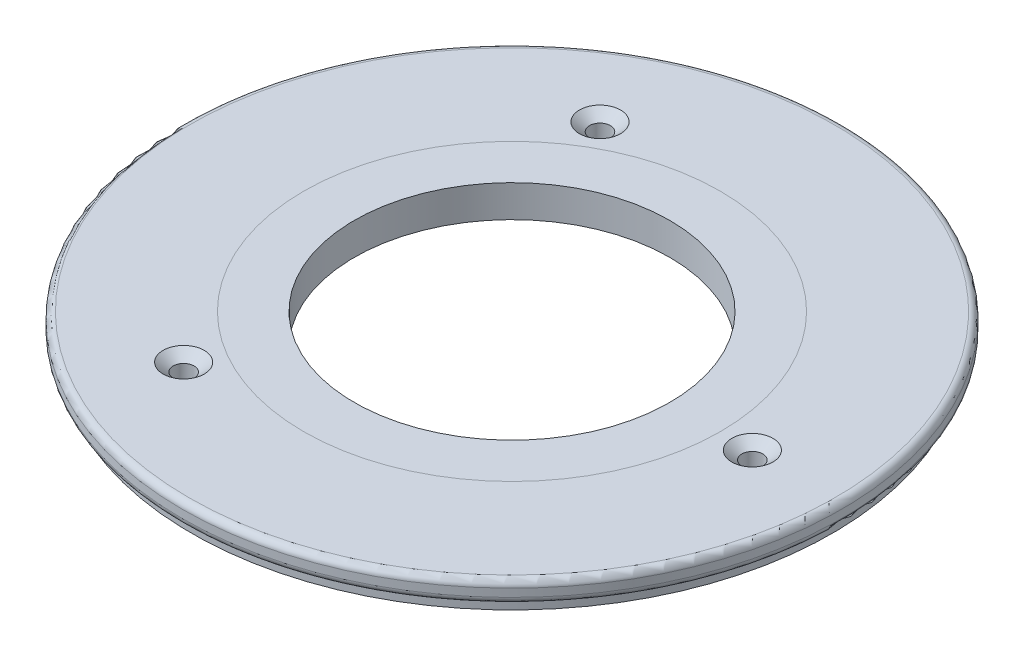
SolidWorks part; units mm, degrees
material "6061-T6 (SS)"
ref_plane "Front Plane" through (0, 0, 0) normal (0, 0, 1) x (1, 0, 0)
ref_plane "Top Plane" through (0, 0, 0) normal (0, 1, 0) x (1, 0, 0)
ref_plane "Right Plane" through (0, 0, 0) normal (1, 0, 0) x (0, 0, -1)
sketch "Sketch1" plane through (0, 0, 0) normal (0, 1, 0) x (1, 0, 0)
  circle A0 centre (0, 0) radius 78.359
  circle A1 centre (0, 0) radius 37.5031
  dimension "D1" = 75.0062
  dimension "D2" = 156.718
extrude "Boss-Extrude1" add sketch "Sketch1" along normal blind 7.62
hole_wizard "CSK for #10 Flat Head Machine Screw (100)1" positions "Sketch4" profile "Sketch5" countersink size "#10" standard "ANSI Inch" end condition through all
sketch "Sketch4" plane through (0, 7.62, 0) normal (0, 1, 0) x (1, 0, 0)
  line L0 (-65.4508, 0) -> (95.8403, 0) construction
  point P0 (57.15, 0)
  dimension "D1" = 57.15
sketch "Sketch5" plane through (57.15, 7.62, 0) normal (1, 0, 0) x (0, 0, 1)
  line L0 (0, 0) -> (0, 7.62)
  line L1 (0, 7.62) -> (2.4892, 7.62)
  line L2 (2.4892, 7.62) -> (2.4892, 2.0141)
  line L3 (2.4892, 2.0141) -> (4.8895, 0)
  line L5 (4.8895, 0) -> (0, 0)
  line L6 (-2.4892, 2.0141) -> (-4.8895, 0) construction
  line L11 (0, -6.35) -> (0, 107.95) construction
  dimension "Thru Hole Dia." = 4.9784
  dimension "Thru Hole Depth" = 7.62
  dimension "Near C'Sink Dia." = 9.779
  dimension "Near C'Sink Angle" = 100
pattern_circular "CirPattern1" count 4 every 120 about axis through (0, 0, 0) along (0, 1, 0) of "CSK for #10 Flat Head Machine Screw (100)1"
sketch "Sketch6" plane through (0, 0, 0) normal (0, -1, 0) x (1, 0, 0)
  circle A0 centre (0, 0) radius 76.1746
  circle A1 centre (0, 0) radius 78.359
  dimension "D2" = 156.718
  dimension "D1" = 152.3492
extrude "Cut-Extrude1" cut sketch "Sketch6" against normal blind 2.54
fillet "Fillet1" radius 1.5875 2 edges at (0, 2.54, -78.359) (0, 7.62, 78.359)
sketch "Sketch7" plane through (0, 7.62, 0) normal (0, 1, 0) x (1, 0, 0)
  circle A0 centre (0, 0) radius 49.53
  dimension "D1" = 99.06
split line "Split Line1"
equation "\"ID\"= 2.953in"
equation "\"D1@Sketch1\"=\"ID\""
equation "\"OD\"= 6.17in"
equation "\"h\"= 0.3"
equation "\"D1@Boss-Extrude1\"=\"h\""
equation "\"HoleDist\"= 2.25"
equation "\"D1@Sketch4\"=\"HoleDist\""
equation "\"D2@Sketch1\"=\"OD\""
equation "\"CouplerDia\"= 5.998"
equation "\"D1@Sketch6\"=\"CouplerDia\""
equation "\"D2@Sketch6\"=\"OD\""
